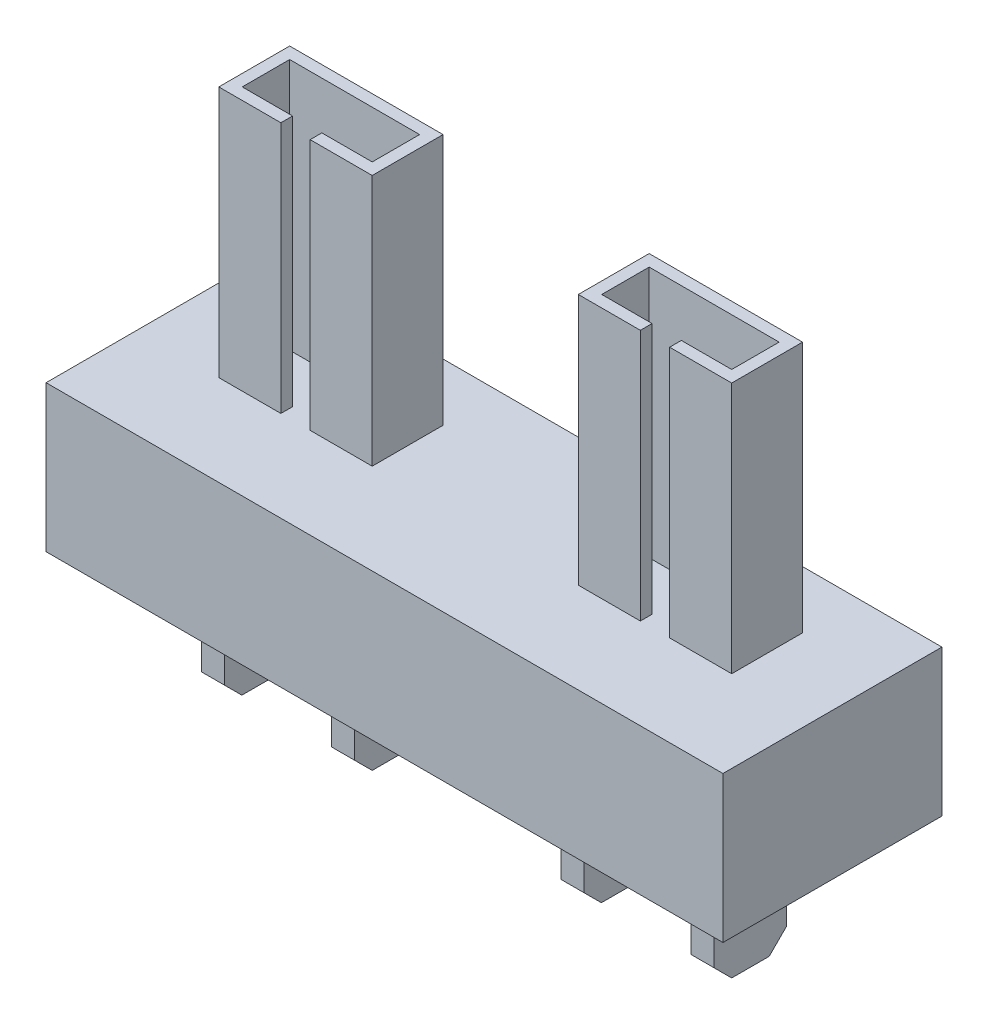
SolidWorks part; units mm, degrees
ref_plane "Front Plane" through (0, 0, 0) normal (0, 0, 1) x (1, 0, 0)
ref_plane "Top Plane" through (0, 0, 0) normal (0, 1, 0) x (1, 0, 0)
ref_plane "Right Plane" through (0, 0, 0) normal (1, 0, 0) x (0, 0, -1)
sketch "Sketch1" plane through (0, 0, 0) normal (0, 0, 1) x (1, 0, 0)
  line L1 (-7.3406, -1.5875) -> (7.3406, -1.5875)
  line L2 (-7.3406, -1.5875) -> (-7.3406, 1.5875)
  line L3 (-7.3406, 1.5875) -> (7.3406, 1.5875)
  line L4 (7.3406, -1.5875) -> (7.3406, 1.5875)
  line L5 (-7.3406, -1.5875) -> (7.3406, 1.5875) construction
  line L6 (-7.3406, 1.5875) -> (7.3406, -1.5875) construction
  point P0 (0, 0)
  dimension "D1" = 3.175
  dimension "D2" = 14.6812
extrude "Boss-Extrude1" add sketch "Sketch1" along normal mid plane 4.7498
sketch "Sketch2" plane through (0, -1.5875, 0) normal (0, -1, 0) x (1, 0, 0)
  line L0 (-7.3406, 2.3749) -> (-7.3406, -2.3749) construction
  line L1 (-5.5622, 0.7874) -> (-5.0622, 0.7874)
  line L2 (-5.5622, 0.7874) -> (-5.5622, -0.7874)
  line L3 (-5.5622, -0.7874) -> (-5.0622, -0.7874)
  line L4 (-5.0622, 0.7874) -> (-5.0622, -0.7874)
  line L5 (-2.7352, 0.7874) -> (-2.2352, 0.7874)
  line L6 (-2.7352, 0.7874) -> (-2.7352, -0.7874)
  line L7 (-2.7352, -0.7874) -> (-2.2352, -0.7874)
  line L8 (-2.2352, 0.7874) -> (-2.2352, -0.7874)
  line L9 (0, 2.3749) -> (0, 0) construction
  line L10 (-7.3406, 2.3749) -> (7.3406, 2.3749) construction
  line L11 (2.2352, 0.7874) -> (2.2352, -0.7874)
  line L12 (2.7352, 0.7874) -> (2.2352, 0.7874)
  line L13 (2.7352, 0.7874) -> (2.7352, -0.7874)
  line L14 (2.7352, -0.7874) -> (2.2352, -0.7874)
  line L15 (5.5622, -0.7874) -> (5.0622, -0.7874)
  line L16 (5.0622, 0.7874) -> (5.0622, -0.7874)
  line L17 (-7.3406, 0) -> (7.3406, 0) construction
  line L18 (7.3406, 2.3749) -> (7.3406, -2.3749) construction
  line L19 (5.5622, 0.7874) -> (5.0622, 0.7874)
  line L20 (5.5622, 0.7874) -> (5.5622, -0.7874)
  line L21 (5.3122, -0.7874) -> (5.3122, 0.7874) construction
  line L22 (2.4852, -0.7874) -> (2.4852, 0.7874) construction
  line L23 (-2.4852, -0.7874) -> (-2.4852, 0.7874) construction
  line L24 (-5.3122, -0.7874) -> (-5.3122, 0.7874) construction
  point P22 (-5.5622, 0)
  dimension "D1" = 10.6244
  dimension "D2" = 0.5
  dimension "D3" = 1.5748
extrude "Boss-Extrude2" add sketch "Sketch2" along normal blind 2.54
chamfer "Chamfer1" distance 0.381 angle 45 8 edges at (-5.3122, -4.1275, -0.7874) (-2.4852, -4.1275, -0.7874) (2.4852, -4.1275, -0.7874) (5.3122, -4.1275, -0.7874) (-5.3122, -4.1275, 0.7874) (-2.4852, -4.1275, 0.7874) (2.4852, -4.1275, 0.7874) (5.3122, -4.1275, 0.7874)
sketch "Sketch3" plane through (0, 1.5875, 0) normal (0, 1, 0) x (1, 0, 0)
  line L0 (-2.2352, 0.7874) -> (-2.2352, -0.7874) construction
  line L1 (-5.5622, 1.1303) -> (-2.2352, 1.1303) construction
  line L2 (-5.5622, 1.1303) -> (-5.5622, -0.7874) construction
  line L3 (-5.5622, -0.7874) -> (-2.2352, -0.7874) construction
  line L4 (-2.2352, 1.1303) -> (-2.2352, -0.7874) construction
  line L5 (-5.5622, -0.7874) -> (-5.5622, 0.7874) construction
  line L6 (7.3406, 2.3749) -> (-7.3406, 2.3749) construction
  line L7 (-5.3082, 0.8763) -> (-2.4892, 0.8763)
  line L8 (-5.5622, 1.1303) -> (-2.2352, 1.1303)
  line L9 (-5.5622, 1.1303) -> (-5.5622, -0.4064)
  line L10 (-5.5622, -0.4064) -> (-4.2162, -0.4064)
  line L11 (-2.2352, 1.1303) -> (-2.2352, -0.4064)
  line L12 (-2.4892, 0.8763) -> (-2.4892, -0.1524)
  line L13 (-5.3082, -0.1524) -> (-4.2162, -0.1524)
  line L14 (-5.3082, 0.8763) -> (-5.3082, -0.1524)
  line L15 (-3.8987, -0.7874) -> (-3.8987, 1.1303) construction
  line L16 (-4.2162, -0.1524) -> (-4.2162, -0.4064)
  line L17 (-3.5812, -0.1524) -> (-3.5812, -0.4064)
  line L18 (-3.5812, -0.1524) -> (-2.4892, -0.1524)
  line L19 (-5.3082, -0.1524) -> (-2.4892, -0.1524) construction
  line L20 (-3.5812, -0.4064) -> (-2.2352, -0.4064)
  line L21 (-5.5622, -0.4064) -> (-2.2352, -0.4064) construction
  line L23 (5.5622, 1.1303) -> (5.5622, -0.4064)
  line L24 (2.2352, 1.1303) -> (5.5622, 1.1303)
  line L25 (2.2352, 1.1303) -> (2.2352, -0.4064)
  line L26 (2.2352, -0.4064) -> (3.5812, -0.4064)
  line L27 (3.5812, -0.1524) -> (3.5812, -0.4064)
  line L28 (2.4892, -0.1524) -> (3.5812, -0.1524)
  line L29 (2.4892, 0.8763) -> (2.4892, -0.1524)
  line L30 (2.4892, 0.8763) -> (5.3082, 0.8763)
  line L31 (5.3082, 0.8763) -> (5.3082, -0.1524)
  line L32 (4.2162, -0.1524) -> (5.3082, -0.1524)
  line L33 (4.2162, -0.1524) -> (4.2162, -0.4064)
  line L34 (4.2162, -0.4064) -> (5.5622, -0.4064)
  dimension "D1" = 1.2446
  dimension "D5" = 0.381
  dimension "D3" = 0.635
  dimension "D4" = 2
  dimension "D2" = 0.254
extrude "Boss-Extrude3" add sketch "Sketch3" along normal blind 5.461
sketch "Sketch4" plane through (0, 7.0485, 0) normal (0, 1, 0) x (1, 0, 0)
  line L0 (-5.3082, 0.8763) -> (-2.4892, -0.1524) construction
  line L1 (5.3082, 0.8763) -> (2.4892, -0.1524) construction
  circle A0 centre (-3.8987, 0.3619) radius 1.5875 construction
  circle A1 centre (3.8987, 0.362) radius 1.5875 construction
  dimension "D1" = 3.175
sketch "Sketch5" plane through (0, -1.5875, 0) normal (0, -1, 0) x (1, 0, 0)
  line L0 (-5.5622, 0) -> (-5.0622, 0) construction
  line L1 (-5.5622, 0.4064) -> (-5.5622, -0.4064) construction
  line L2 (-5.0622, -0.4064) -> (-5.0622, 0.4064) construction
  line L3 (-2.7352, 0) -> (5.5622, 0) construction
  line L4 (-2.7352, 0.4064) -> (-2.7352, -0.4064) construction
  line L5 (5.5622, -0.4064) -> (5.5622, 0.4064) construction
  circle A0 centre (-5.3122, 0) radius 1.5875 construction
  circle A1 centre (-3.8987, -0.3619) radius 1.5875 construction
